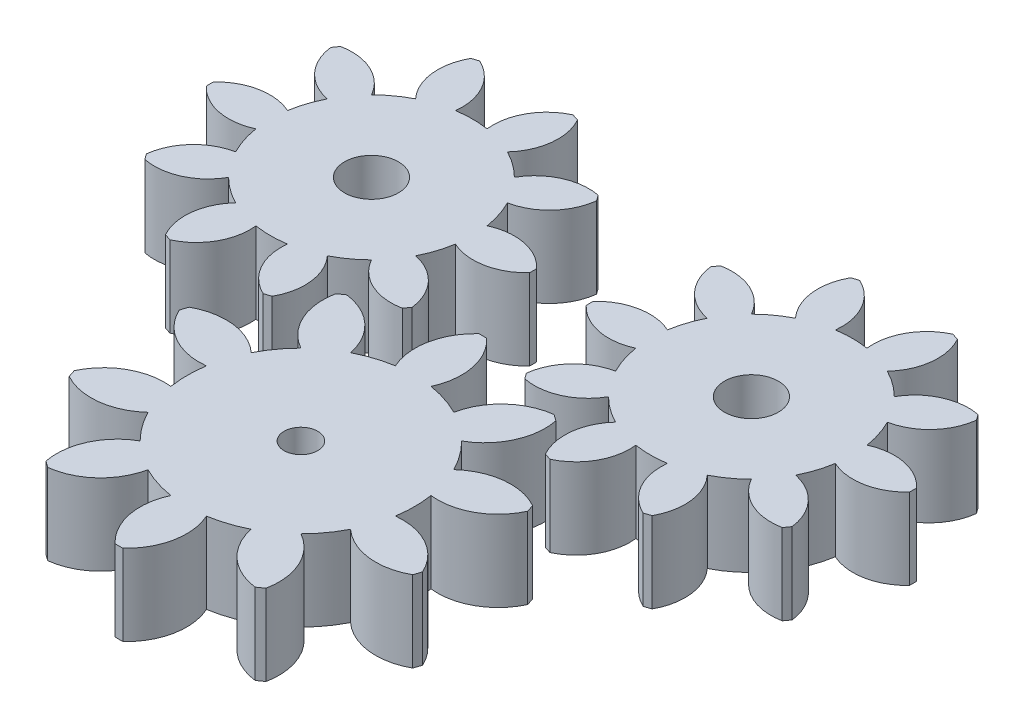
SolidWorks part; units mm, degrees
ref_plane "Front Plane" through (0, 0, 0) normal (0, 0, 1) x (1, 0, 0)
ref_plane "Top Plane" through (0, 0, 0) normal (0, 1, 0) x (1, 0, 0)
ref_plane "Right Plane" through (0, 0, 0) normal (1, 0, 0) x (0, 0, -1)
sketch "Sketch1" plane through (0, 0, 0) normal (0, 1, 0) x (1, 0, 0)
  point P0 (0, 0)
  circle B0 centre (44.5736, 30.0605) radius 2.5
  arc B1 (45.1595, 57.0541) -> (43.9877, 57.0541) centre (44.5736, 30.0605) ccw
  arc B2 (47.2173, 46.7261) -> (45.1595, 57.0541) centre (39.0302, 50.4639) ccw
  arc B3 (52.2306, 45.0972) -> (47.2173, 46.7261) centre (44.5736, 30.0605) ccw
  arc B4 (59.966, 52.2432) -> (52.2306, 45.0972) centre (61.0512, 43.3089) ccw
  arc B5 (60.9141, 51.5544) -> (59.966, 52.2432) centre (44.5736, 30.0605) ccw
  arc B6 (56.5082, 41.9894) -> (60.9141, 51.5544) centre (52.0817, 49.8256) ccw
  arc B7 (59.6066, 37.7247) -> (56.5082, 41.9894) centre (44.5736, 30.0605) ccw
  arc B8 (70.065, 38.9592) -> (59.6066, 37.7247) centre (65.6914, 31.0934) ccw
  arc B9 (70.4271, 37.8447) -> (70.065, 38.9592) centre (44.5736, 30.0605) ccw
  arc B10 (61.2405, 32.6962) -> (70.4271, 37.8447) centre (62.2654, 41.6376) ccw
  arc B11 (61.2405, 27.4248) -> (61.2405, 32.6962) centre (44.5736, 30.0605) ccw
  arc B12 (70.4271, 22.2763) -> (61.2405, 27.4248) centre (62.2654, 18.4834) ccw
  arc B13 (70.065, 21.1617) -> (70.4271, 22.2763) centre (44.5736, 30.0605) ccw
  arc B14 (59.6066, 22.3963) -> (70.065, 21.1617) centre (65.6914, 29.0276) ccw
  arc B15 (56.5082, 18.1316) -> (59.6066, 22.3963) centre (44.5736, 30.0605) ccw
  arc B16 (60.9141, 8.5666) -> (56.5082, 18.1316) centre (52.0817, 10.2954) ccw
  arc B17 (59.966, 7.8778) -> (60.9141, 8.5666) centre (44.5736, 30.0605) ccw
  arc B18 (52.2306, 15.0238) -> (59.966, 7.8778) centre (61.0512, 16.8121) ccw
  arc B19 (47.2173, 13.3949) -> (52.2306, 15.0238) centre (44.5736, 30.0605) ccw
  arc B20 (45.1595, 3.0668) -> (47.2173, 13.3949) centre (39.0302, 9.6571) ccw
  arc B21 (43.9877, 3.0668) -> (45.1595, 3.0668) centre (44.5736, 30.0605) ccw
  arc B22 (41.9299, 13.3949) -> (43.9877, 3.0668) centre (50.117, 9.6571) ccw
  arc B23 (36.9166, 15.0238) -> (41.9299, 13.3949) centre (44.5736, 30.0605) ccw
  arc B24 (29.1812, 7.8778) -> (36.9166, 15.0238) centre (28.096, 16.8121) ccw
  arc B25 (28.2331, 8.5666) -> (29.1812, 7.8778) centre (44.5736, 30.0605) ccw
  arc B26 (32.639, 18.1316) -> (28.2331, 8.5666) centre (37.0655, 10.2954) ccw
  arc B27 (29.5406, 22.3963) -> (32.639, 18.1316) centre (44.5736, 30.0605) ccw
  arc B28 (19.0822, 21.1617) -> (29.5406, 22.3963) centre (23.4558, 29.0276) ccw
  arc B29 (18.7201, 22.2763) -> (19.0822, 21.1617) centre (44.5736, 30.0605) ccw
  arc B30 (27.9067, 27.4248) -> (18.7201, 22.2763) centre (26.8818, 18.4834) ccw
  arc B31 (27.9067, 32.6962) -> (27.9067, 27.4248) centre (44.5736, 30.0605) ccw
  arc B32 (18.7201, 37.8447) -> (27.9067, 32.6962) centre (26.8818, 41.6376) ccw
  arc B33 (19.0822, 38.9592) -> (18.7201, 37.8447) centre (44.5736, 30.0605) ccw
  arc B34 (29.5406, 37.7247) -> (19.0822, 38.9592) centre (23.4558, 31.0934) ccw
  arc B35 (32.639, 41.9894) -> (29.5406, 37.7247) centre (44.5736, 30.0605) ccw
  arc B36 (28.2331, 51.5544) -> (32.639, 41.9894) centre (37.0655, 49.8256) ccw
  arc B37 (29.1812, 52.2432) -> (28.2331, 51.5544) centre (44.5736, 30.0605) ccw
  arc B38 (36.9166, 45.0972) -> (29.1812, 52.2432) centre (28.096, 43.3089) ccw
  arc B39 (41.9299, 46.7261) -> (36.9166, 45.0972) centre (44.5736, 30.0605) ccw
  arc B40 (43.9877, 57.0541) -> (41.9299, 46.7261) centre (50.117, 50.4639) ccw
sketch_block_instance "Block1-1"
sketch_block "Block1"
sketch "Sketch2" plane through (0, 0, 0) normal (0, 1, 0) x (1, 0, 0)
  circle B0 centre (15.9251, 69.1831) radius 4
  arc B1 (39.9193, 68.6545) -> (39.9193, 69.7117) centre (15.9251, 69.1831) ccw
  arc B2 (30.7381, 66.8284) -> (39.9193, 68.6545) centre (34.0631, 74.1047) ccw
  arc B3 (29.2931, 62.3812) -> (30.7381, 66.8284) centre (15.9251, 69.1831) ccw
  arc B4 (35.6475, 55.5074) -> (29.2931, 62.3812) centre (27.7062, 54.5402) ccw
  arc B5 (35.0261, 54.652) -> (35.6475, 55.5074) centre (15.9251, 69.1831) ccw
  arc B6 (26.525, 58.5713) -> (35.0261, 54.652) centre (33.4919, 62.5036) ccw
  arc B7 (22.742, 55.8227) -> (26.525, 58.5713) centre (15.9251, 69.1831) ccw
  arc B8 (23.8425, 46.5267) -> (22.742, 55.8227) centre (16.8493, 50.412) ccw
  arc B9 (22.837, 46.2) -> (23.8425, 46.5267) centre (15.9251, 69.1831) ccw
  arc B10 (18.2631, 54.3675) -> (22.837, 46.2) centre (26.2108, 53.4537) ccw
  arc B11 (13.5871, 54.3675) -> (18.2631, 54.3675) centre (15.9251, 69.1831) ccw
  arc B12 (9.0132, 46.2) -> (13.5871, 54.3675) centre (5.6394, 53.4537) ccw
  arc B13 (8.0078, 46.5267) -> (9.0132, 46.2) centre (15.9251, 69.1831) ccw
  arc B14 (9.1082, 55.8227) -> (8.0078, 46.5267) centre (15.0009, 50.412) ccw
  arc B15 (5.3252, 58.5713) -> (9.1082, 55.8227) centre (15.9251, 69.1831) ccw
  arc B16 (-3.1759, 54.652) -> (5.3252, 58.5713) centre (-1.6417, 62.5036) ccw
  arc B17 (-3.7973, 55.5074) -> (-3.1759, 54.652) centre (15.9251, 69.1831) ccw
  arc B18 (2.5571, 62.3812) -> (-3.7973, 55.5074) centre (4.144, 54.5402) ccw
  arc B19 (1.1121, 66.8284) -> (2.5571, 62.3812) centre (15.9251, 69.1831) ccw
  arc B20 (-8.0691, 68.6545) -> (1.1121, 66.8284) centre (-2.2129, 74.1047) ccw
  arc B21 (-8.0691, 69.7117) -> (-8.0691, 68.6545) centre (15.9251, 69.1831) ccw
  arc B22 (1.1121, 71.5378) -> (-8.0691, 69.7117) centre (-2.2129, 64.2615) ccw
  arc B23 (2.5571, 75.985) -> (1.1121, 71.5378) centre (15.9251, 69.1831) ccw
  arc B24 (-3.7973, 82.8589) -> (2.5571, 75.985) centre (4.144, 83.826) ccw
  arc B25 (-3.1759, 83.7142) -> (-3.7973, 82.8589) centre (15.9251, 69.1831) ccw
  arc B26 (5.3252, 79.795) -> (-3.1759, 83.7142) centre (-1.6417, 75.8627) ccw
  arc B27 (9.1082, 82.5435) -> (5.3252, 79.795) centre (15.9251, 69.1831) ccw
  arc B28 (8.0078, 91.8396) -> (9.1082, 82.5435) centre (15.0009, 87.9542) ccw
  arc B29 (9.0132, 92.1663) -> (8.0078, 91.8396) centre (15.9251, 69.1831) ccw
  arc B30 (13.5871, 83.9988) -> (9.0132, 92.1663) centre (5.6394, 84.9125) ccw
  arc B31 (18.2631, 83.9988) -> (13.5871, 83.9988) centre (15.9251, 69.1831) ccw
  arc B32 (22.837, 92.1663) -> (18.2631, 83.9988) centre (26.2108, 84.9125) ccw
  arc B33 (23.8425, 91.8396) -> (22.837, 92.1663) centre (15.9251, 69.1831) ccw
  arc B34 (22.742, 82.5435) -> (23.8425, 91.8396) centre (16.8493, 87.9542) ccw
  arc B35 (26.525, 79.795) -> (22.742, 82.5435) centre (15.9251, 69.1831) ccw
  arc B36 (35.0261, 83.7142) -> (26.525, 79.795) centre (33.4919, 75.8627) ccw
  arc B37 (35.6475, 82.8589) -> (35.0261, 83.7142) centre (15.9251, 69.1831) ccw
  arc B38 (29.2931, 75.985) -> (35.6475, 82.8589) centre (27.7062, 83.826) ccw
  arc B39 (30.7381, 71.5378) -> (29.2931, 75.985) centre (15.9251, 69.1831) ccw
  arc B40 (39.9193, 69.7117) -> (30.7381, 71.5378) centre (34.0631, 64.2615) ccw
  circle B41 centre (72.3122, 69.1831) radius 4
  arc B42 (96.3064, 68.6545) -> (96.3064, 69.7117) centre (72.3122, 69.1831) ccw
  arc B43 (87.1252, 66.8284) -> (96.3064, 68.6545) centre (90.4502, 74.1047) ccw
  arc B44 (85.6802, 62.3812) -> (87.1252, 66.8284) centre (72.3122, 69.1831) ccw
  arc B45 (92.0346, 55.5074) -> (85.6802, 62.3812) centre (84.0933, 54.5402) ccw
  arc B46 (91.4132, 54.652) -> (92.0346, 55.5074) centre (72.3122, 69.1831) ccw
  arc B47 (82.9121, 58.5713) -> (91.4132, 54.652) centre (89.879, 62.5036) ccw
  arc B48 (79.1291, 55.8227) -> (82.9121, 58.5713) centre (72.3122, 69.1831) ccw
  arc B49 (80.2295, 46.5267) -> (79.1291, 55.8227) centre (73.2364, 50.412) ccw
  arc B50 (79.2241, 46.2) -> (80.2295, 46.5267) centre (72.3122, 69.1831) ccw
  arc B51 (74.6502, 54.3675) -> (79.2241, 46.2) centre (82.5979, 53.4537) ccw
  arc B52 (69.9742, 54.3675) -> (74.6502, 54.3675) centre (72.3122, 69.1831) ccw
  arc B53 (65.4003, 46.2) -> (69.9742, 54.3675) centre (62.0265, 53.4537) ccw
  arc B54 (64.3948, 46.5267) -> (65.4003, 46.2) centre (72.3122, 69.1831) ccw
  arc B55 (65.4953, 55.8227) -> (64.3948, 46.5267) centre (71.388, 50.412) ccw
  arc B56 (61.7123, 58.5713) -> (65.4953, 55.8227) centre (72.3122, 69.1831) ccw
  arc B57 (53.2112, 54.652) -> (61.7123, 58.5713) centre (54.7454, 62.5036) ccw
  arc B58 (52.5898, 55.5074) -> (53.2112, 54.652) centre (72.3122, 69.1831) ccw
  arc B59 (58.9442, 62.3812) -> (52.5898, 55.5074) centre (60.5311, 54.5402) ccw
  arc B60 (57.4992, 66.8284) -> (58.9442, 62.3812) centre (72.3122, 69.1831) ccw
  arc B61 (48.318, 68.6545) -> (57.4992, 66.8284) centre (54.1742, 74.1047) ccw
  arc B62 (48.318, 69.7117) -> (48.318, 68.6545) centre (72.3122, 69.1831) ccw
  arc B63 (57.4992, 71.5378) -> (48.318, 69.7117) centre (54.1742, 64.2615) ccw
  arc B64 (58.9442, 75.985) -> (57.4992, 71.5378) centre (72.3122, 69.1831) ccw
  arc B65 (52.5898, 82.8589) -> (58.9442, 75.985) centre (60.5311, 83.826) ccw
  arc B66 (53.2112, 83.7142) -> (52.5898, 82.8589) centre (72.3122, 69.1831) ccw
  arc B67 (61.7123, 79.795) -> (53.2112, 83.7142) centre (54.7454, 75.8627) ccw
  arc B68 (65.4953, 82.5435) -> (61.7123, 79.795) centre (72.3122, 69.1831) ccw
  arc B69 (64.3948, 91.8396) -> (65.4953, 82.5435) centre (71.388, 87.9542) ccw
  arc B70 (65.4003, 92.1663) -> (64.3948, 91.8396) centre (72.3122, 69.1831) ccw
  arc B71 (69.9742, 83.9988) -> (65.4003, 92.1663) centre (62.0265, 84.9125) ccw
  arc B72 (74.6502, 83.9988) -> (69.9742, 83.9988) centre (72.3122, 69.1831) ccw
  arc B73 (79.2241, 92.1663) -> (74.6502, 83.9988) centre (82.5979, 84.9125) ccw
  arc B74 (80.2295, 91.8396) -> (79.2241, 92.1663) centre (72.3122, 69.1831) ccw
  arc B75 (79.1291, 82.5435) -> (80.2295, 91.8396) centre (73.2364, 87.9542) ccw
  arc B76 (82.9121, 79.795) -> (79.1291, 82.5435) centre (72.3122, 69.1831) ccw
  arc B77 (91.4132, 83.7142) -> (82.9121, 79.795) centre (89.879, 75.8627) ccw
  arc B78 (92.0346, 82.8589) -> (91.4132, 83.7142) centre (72.3122, 69.1831) ccw
  arc B79 (85.6802, 75.985) -> (92.0346, 82.8589) centre (84.0933, 83.826) ccw
  arc B80 (87.1252, 71.5378) -> (85.6802, 75.985) centre (72.3122, 69.1831) ccw
  arc B81 (96.3064, 69.7117) -> (87.1252, 71.5378) centre (90.4502, 64.2615) ccw
sketch_block_instance "Block2-1"
sketch_block "Block2"
sketch_block_instance "Block2-2"
extrude "Boss-Extrude1" add sketch "Sketch2" along normal blind 12
extrude "Boss-Extrude2" add sketch "Sketch1" along normal blind 12 separate body
